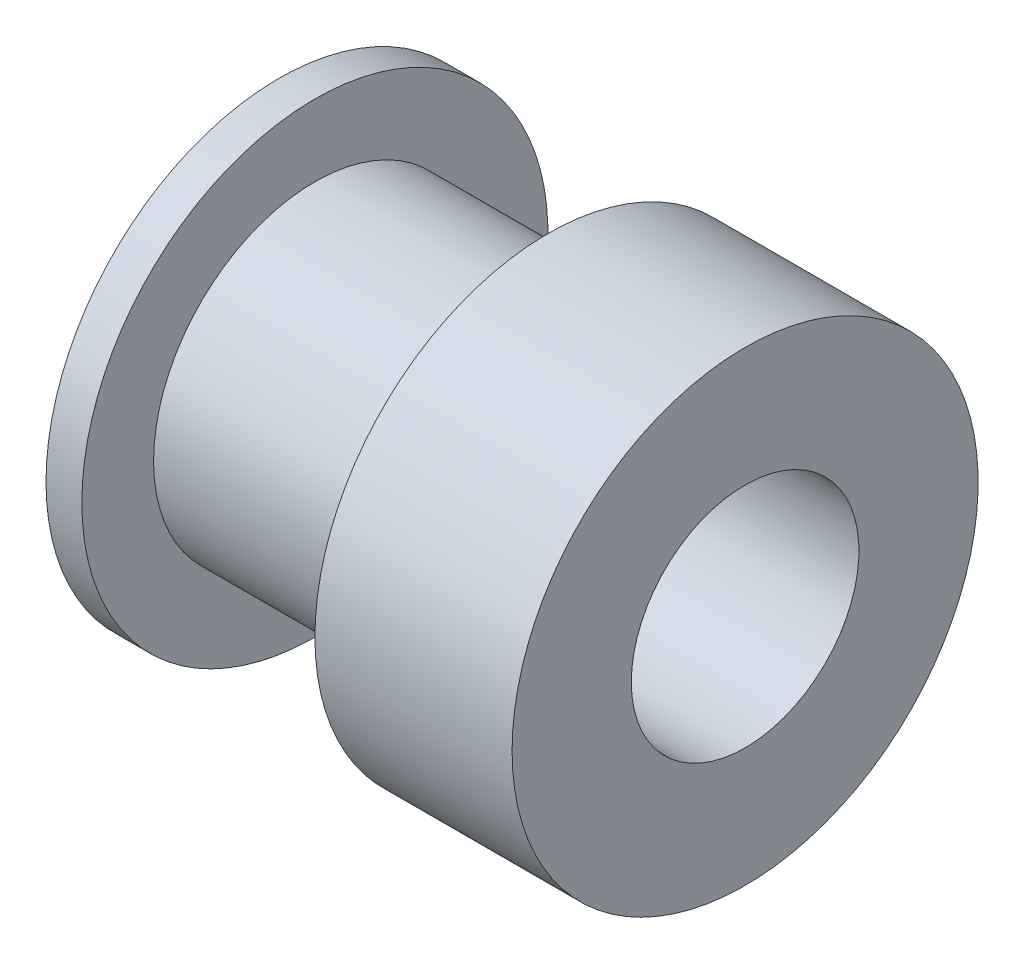
SolidWorks part; units mm, degrees
ref_plane "前视基准面" through (0, 0, 0) normal (0, 0, 1) x (1, 0, 0)
ref_plane "上视基准面" through (0, 0, 0) normal (0, 1, 0) x (1, 0, 0)
ref_plane "右视基准面" through (0, 0, 0) normal (1, 0, 0) x (0, 0, -1)
other "Configuration Table"
sketch "草图1" plane through (0, 0, 0) normal (0, 0, 1) x (1, 0, 0)
  line L0 (6.5, -3.25) -> (-6.5, -3.25)
  line L2 (-6.5, 3.25) -> (-6.5, -3.25)
  line L3 (-6.5, -3.25) -> (6.5, -3.25) construction
  line L4 (6.5, 3.25) -> (6.5, -3.25)
  line L5 (-6.5, 3.25) -> (6.5, -3.25) construction
  line L6 (-6.5, -3.25) -> (6.5, 3.25) construction
  line L7 (-6.5, 3.25) -> (-5.5, 3.25)
  line L8 (-5.5, 3.25) -> (-5.5, 1.25)
  line L9 (-5.5, 1.25) -> (1, 1.25)
  line L10 (1, 1.25) -> (1, 3.25)
  line L11 (1, 3.25) -> (6.5, 3.25)
  point P0 (0, 0)
  dimension "D1" = 13
  dimension "D2" = 6.5
  dimension "D3" = 5.5
  dimension "D4" = 1
  dimension "D5" = 2
  dimension "D6" = 2
revolve "旋转1" add sketch "草图1" angle 360 about L3
sketch "草图2" plane through (-6.5, 0, 0) normal (-1, 0, 0) x (0, 0, 1)
  line L0 (0, 3.25) -> (0, -9.75) construction
  line L1 (-6.5, -3.25) -> (6.5, -3.25) construction
  circle A0 centre (0, -3.25) radius 6.5 construction
  circle A1 centre (0, -3.25) radius 3.175
  point P7 (0, -3.25)
  dimension "D1" = 6.35
extrude "切除-拉伸1" cut sketch "草图2" against normal through all
